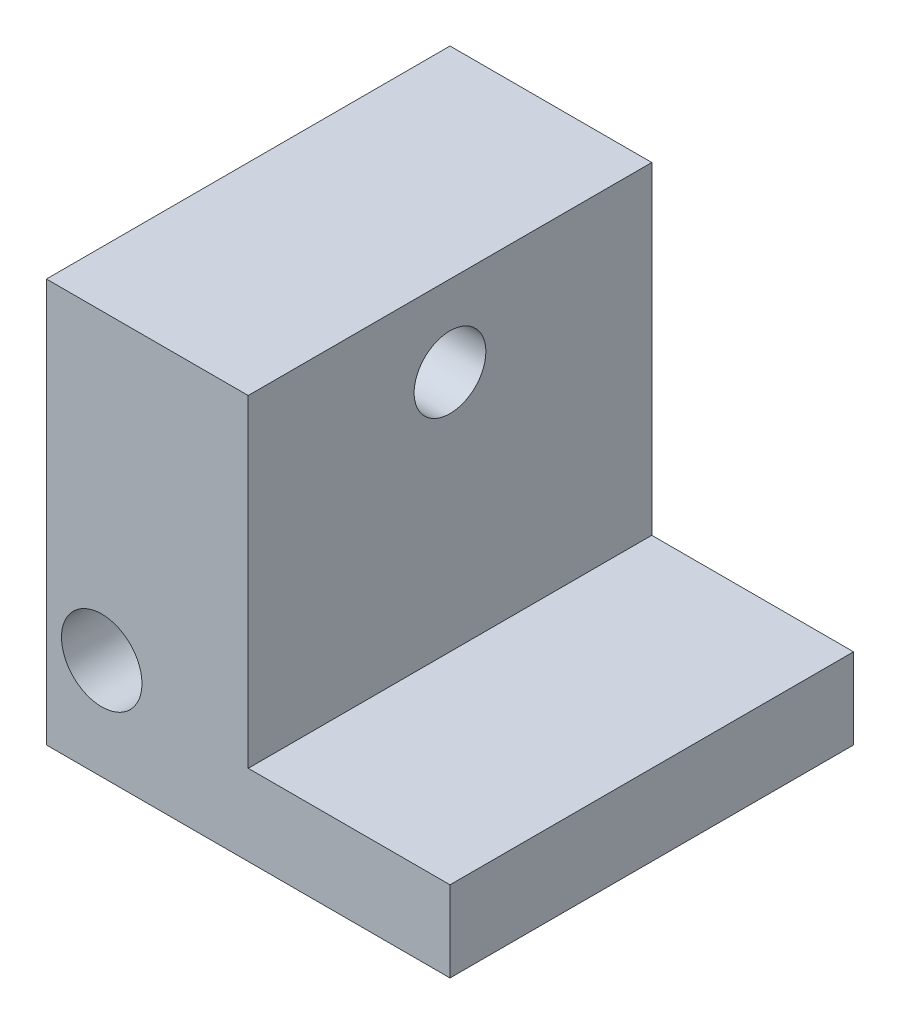
SolidWorks part; units mm, degrees
material "Copper"
ref_plane "Front Plane" through (0, 0, 0) normal (0, 0, 1) x (1, 0, 0)
ref_plane "Top Plane" through (0, 0, 0) normal (0, 1, 0) x (1, 0, 0)
ref_plane "Right Plane" through (0, 0, 0) normal (1, 0, 0) x (0, 0, -1)
sketch "Sketch1" plane through (0, 0, 0) normal (0, 0, 1) x (1, 0, 0)
  line L1 (0, 0) -> (10, 0)
  line L2 (0, 0) -> (0, 10)
  line L3 (0, 10) -> (10, 10)
  line L4 (10, 0) -> (10, 10)
  dimension "D1" = 10
  dimension "D2" = 10
extrude "Extrude1" add sketch "Sketch1" along normal blind 10
sketch "Sketch2" plane through (0, 0, 10) normal (0, 0, 1) x (1, 0, 0)
  line L0 (0, 0) -> (10, 0) construction
  line L1 (10, 10) -> (5, 10)
  line L2 (10, 10) -> (10, 2)
  line L3 (10, 2) -> (5, 2)
  line L4 (5, 10) -> (5, 2)
  dimension "D1" = 2
  dimension "D2" = 5
extrude "Extrude2" cut sketch "Sketch2" against normal through all
sketch "Sketch3" plane through (5, 0, 0) normal (1, 0, 0) x (0, 0, -1)
  line L0 (0, 10) -> (-10, 10) construction
  line L1 (0, 10) -> (0, 2) construction
  circle A0 centre (-5, 8) radius 1
  dimension "D1" = 2
  dimension "D2" = 2
  dimension "D3" = 5
extrude "Extrude3" [suppressed] cut sketch "Sketch3" against normal through all
ref_plane "Plane1" through (0, 0, 5) normal (0, 0, -1) x (-1, 0, 0)
sketch "Sketch4" plane through (0, 0, 0) normal (-1, 0, 0) x (0, 0, 1)
  line L0 (5, 5.5) -> (5, -5.5) construction
  line L2 (10, 0) -> (0, 0) construction
  circle A0 centre (5, 2.5) radius 1.25
  dimension "D1" = 2.5
extrude "Cut-Extrude1" cut sketch "Sketch4" against normal blind 4.5
hole_wizard "#3-48 Tapped Hole1" positions "Sketch6" profile "Sketch5" tap size "#3-48" standard "ANSI Inch"
sketch "Sketch6" plane through (0, 0, 10) normal (0, 0, 1) x (1, 0, 0)
  line L0 (0, 0) -> (10, 0) construction
  line L1 (0, 10) -> (0, 0) construction
  point P0 (1.37, 2.5)
  dimension "D1" = 2.5
  dimension "D2" = 1.37
cosmetic thread "Hole Thread1" parameters "D1"=4.246, "D2"=2.5146
sketch "Sketch5" plane through (1.37, 2.5, 10) normal (1, 0, 0) x (0, -1, 0)
  line L0 (0, 0) -> (0, 5.599)
  line L1 (0, 5.599) -> (0.9969, 5)
  line L2 (0.9969, 5) -> (0.9969, 0)
  line L5 (0.9969, 0) -> (0, 0)
  line L10 (0, 5.599) -> (-0.997, 5) construction
  line L11 (0, -6.35) -> (0, 107.95) construction
  dimension "Tap Drill Dia." = 1.9939
  dimension "Tap Drill Depth" = 5
  dimension "Drill Angle" = 118
hole_wizard "#2-56 Tapped Hole1" positions "Sketch8" profile "Sketch7" tap size "#2-56" standard "ANSI Inch"
sketch "Sketch8" plane through (5, 0, 0) normal (1, 0, 0) x (0, 0, -1)
  line L0 (-5, -5.5) -> (-5, 5.5) construction
  line L1 (0, 10) -> (-10, 10) construction
  point P0 (-5, 8)
  dimension "D1" = 2
cosmetic thread "Hole Thread2" parameters "D1"=4.37, "D2"=2.1844
sketch "Sketch7" plane through (5, 8, 5) normal (0, 1, 0) x (0, 0, -1)
  line L0 (0, 0) -> (0, 6.2642)
  line L1 (0, 6.2642) -> (0.889, 5.73)
  line L2 (0.889, 5.73) -> (0.889, 0)
  line L5 (0.889, 0) -> (0, 0)
  line L10 (0, 6.2642) -> (-0.889, 5.73) construction
  line L11 (0, -6.35) -> (0, 107.95) construction
  dimension "Tap Drill Dia." = 1.778
  dimension "Tap Drill Depth" = 5.73
  dimension "Drill Angle" = 118
